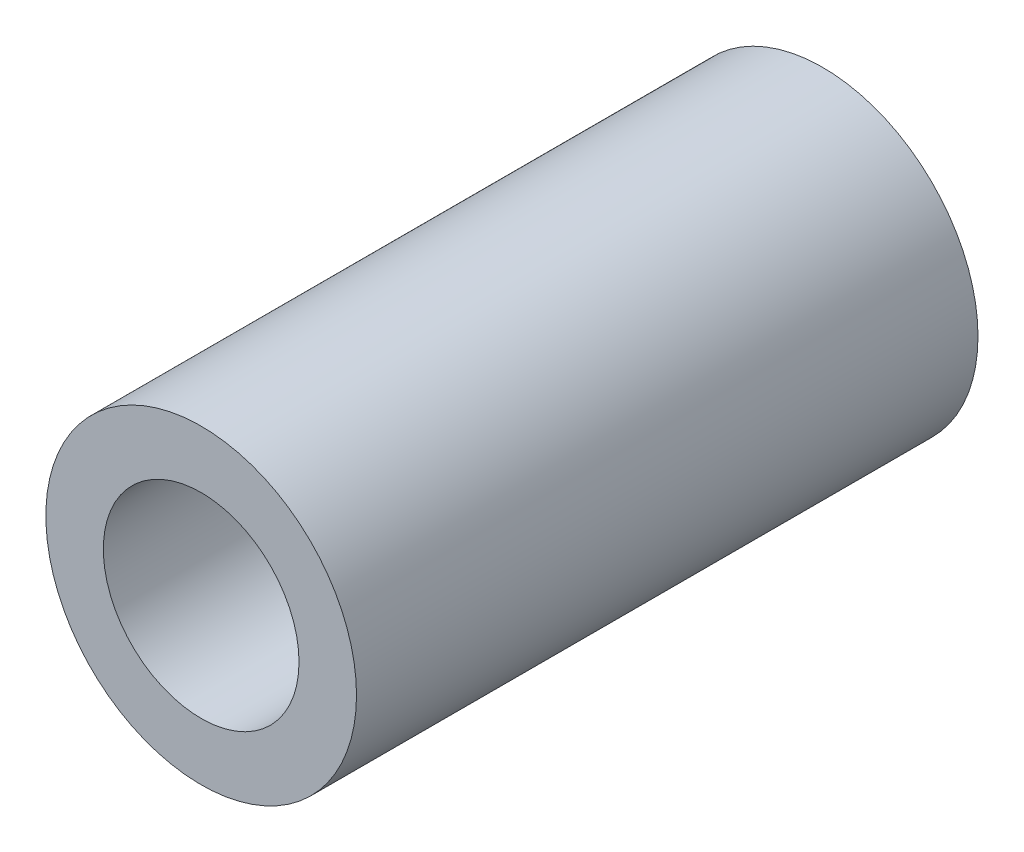
SolidWorks part; units mm, degrees
material "ABS"
ref_plane "Front Plane" through (0, 0, 0) normal (0, 0, 1) x (1, 0, 0)
ref_plane "Top Plane" through (0, 0, 0) normal (0, 1, 0) x (1, 0, 0)
ref_plane "Right Plane" through (0, 0, 0) normal (1, 0, 0) x (0, 0, -1)
sketch "Sketch1" plane through (0, 0, 0) normal (0, 0, 1) x (1, 0, 0)
  circle A0 centre (0, 0) radius 1.5
  circle A1 centre (0, 0) radius 2.3813
  dimension "D1" = 3
  dimension "D2" = 4.7625
extrude "Boss-Extrude1" add sketch "Sketch1" along normal mid plane 9.5275
